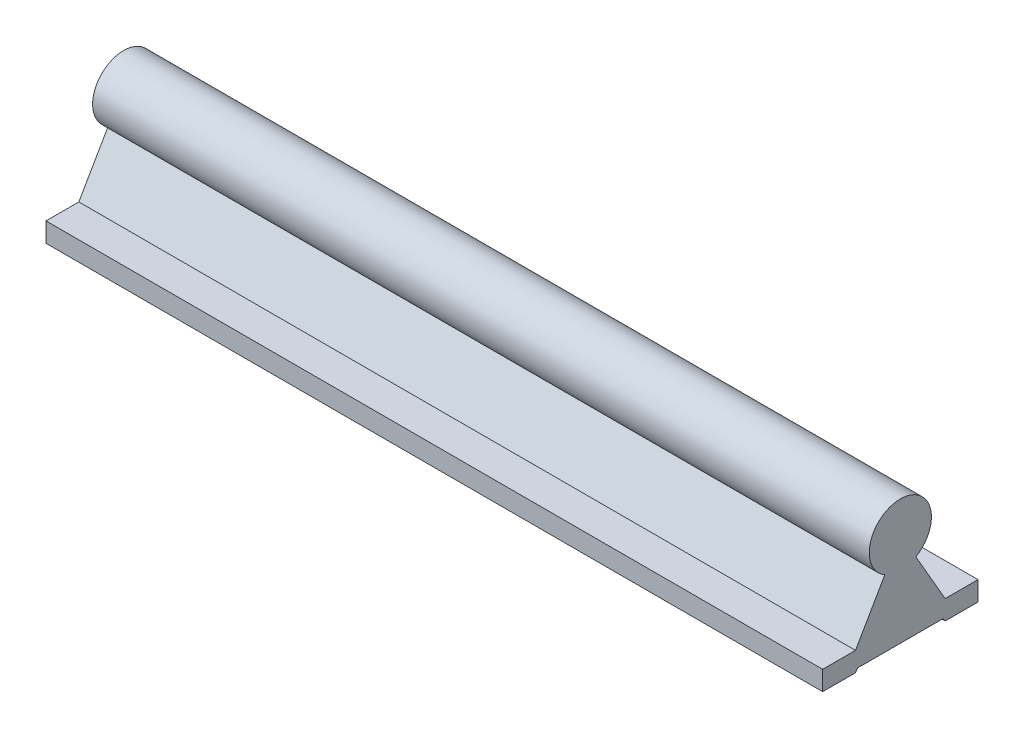
SolidWorks part; units mm, degrees
ref_plane "Front Plane" through (0, 0, 0) normal (0, 0, 1) x (1, 0, 0)
ref_plane "Top Plane" through (0, 0, 0) normal (0, 1, 0) x (1, 0, 0)
ref_plane "Right Plane" through (0, 0, 0) normal (1, 0, 0) x (0, 0, -1)
sketch "Sketch1" plane through (0, 0, 0) normal (1, 0, 0) x (0, 0, -1)
  line L2 (-20, -25) -> (-20, -20)
  line L3 (20, -25) -> (20, -20)
  line L6 (-10.9978, -24.2) -> (10.9978, -24.2)
  line L7 (-11.547, -20) -> (-4, -6.9282)
  line L8 (11.547, -20) -> (4, -6.9282)
  line L9 (-11.547, -25) -> (-10.9978, -24.2)
  line L10 (10.9978, -24.2) -> (11.547, -25)
  line L11 (-20, -25) -> (-11.547, -25)
  line L12 (11.547, -25) -> (20, -25)
  line L13 (-20, -20) -> (-11.547, -20)
  line L14 (11.547, -20) -> (20, -20)
  line L17 (-17.75, -20) -> (-17.75, -25) construction
  line L18 (-12.25, -25) -> (-12.25, -20) construction
  line L20 (12.25, -20) -> (12.25, -25) construction
  line L21 (17.75, -20) -> (17.75, -25) construction
  arc A1 (-4, -6.9282) -> (4, -6.9282) centre (0, 0) cw
  point P1 (0, 0)
  point P4 (0, 0)
  point P7 (0, 0)
  point P13 (0, -24.2)
  point P16 (0, 0)
  point P19 (0, 0)
  point P20 (0, 0)
  point P21 (0, 0)
  point P22 (0, 0)
  point P23 (0, 0)
  point P24 (0, 0)
  point P26 (12.25, -22.6529)
  point P28 (-12.25, -25)
  point P31 (17.75, -22.6529)
  point P32 (-17.75, -25)
  dimension "D1" = 25
  dimension "D2" = 8
  dimension "D3" = 40
  dimension "D4" = 5
  dimension "D5" = 60
extrude "Boss-Extrude1" add sketch "Sketch1" along normal blind 200 contours A1 L8 L14 L3 L12 L10 L6 L9 L11 L2 L13 L7
